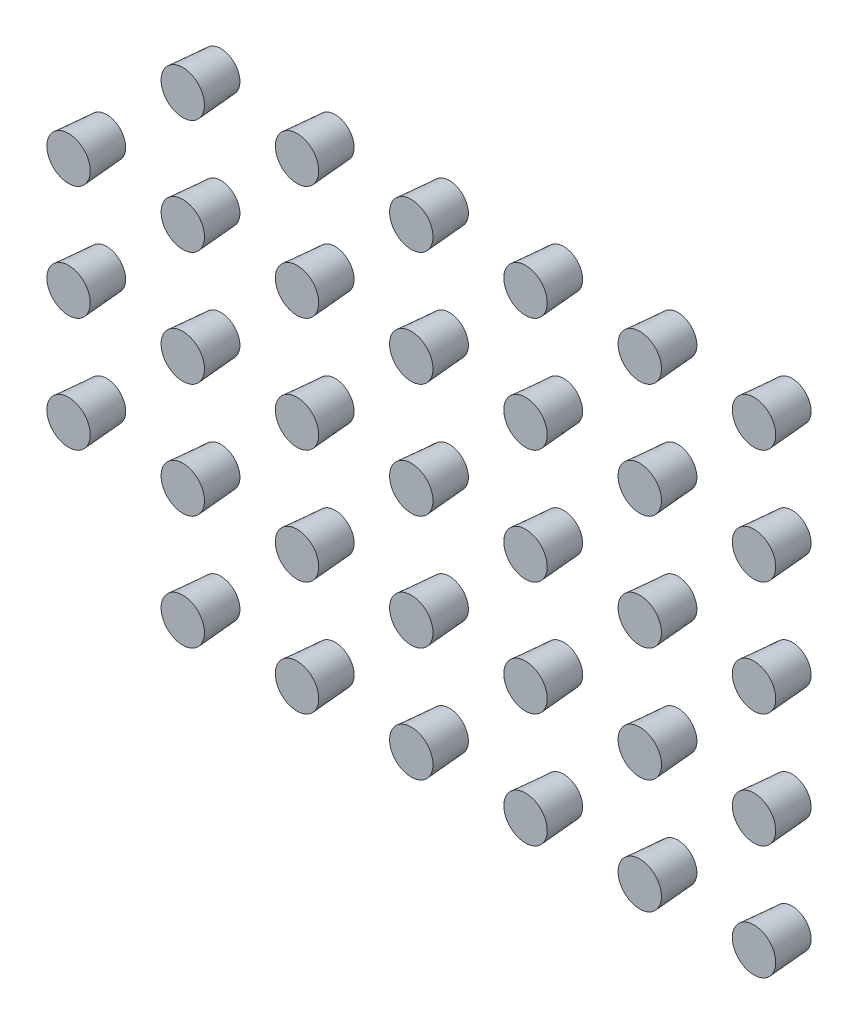
SolidWorks part; units mm, degrees
ref_plane "前视基准面" through (0, 0, 0) normal (0, 0, 1) x (1, 0, 0)
ref_plane "上视基准面" through (0, 0, 0) normal (0, 1, 0) x (1, 0, 0)
ref_plane "右视基准面" through (0, 0, 0) normal (1, 0, 0) x (0, 0, -1)
other "Configuration Table"
sketch "草图1" plane through (0, 0, 0) normal (0, 0, 1) x (1, 0, 0)
  circle A0 centre (0, 0) radius 0.5
  dimension "D1" = 1
extrude "凸台-拉伸1" add sketch "草图1" along normal blind 1 draft 4 draft outward yes
pattern_linear "阵列(线性)1" count 6 spacing 3 along (0, 1, 0) count 6 spacing 3 along (1, 0, 0) of "凸台-拉伸1"
ref_plane "基准面1" through (7.5, 0, 0) normal (1, 0, 0) x (0, 0, -1)
ref_plane "基准面2" through (0, 7.5, 0) normal (0, 1, 0) x (1, 0, 0)
pattern_linear "阵列(线性)2" count 2 spacing 3 along (-1, 0, 0) of bodies 110 109 108 107
pattern_linear "阵列(线性)3" count 2 spacing 3 along (-1, 0, 0) of bodies 143 144
delete or keep bodies "实体-删除/保留 1" type keep bodies bodies 123 140 117 134 111 128 122 139 116 133 110 127 144 121 138 115 132 109 126 143 120 137 114 131 108 125 142 119 113 107 141 135 129
